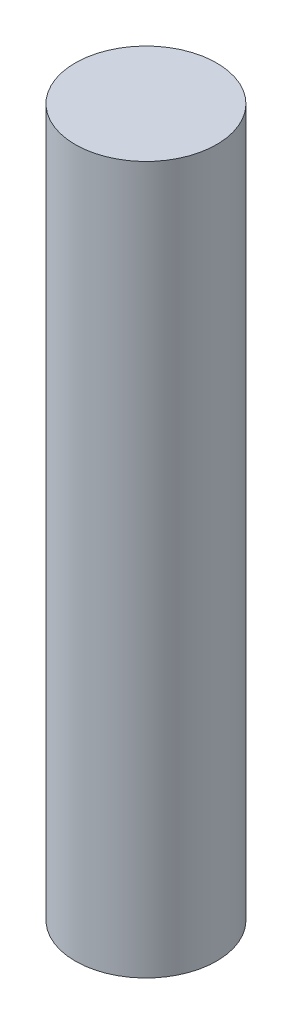
SolidWorks part; units mm, degrees
ref_plane "Front Plane" through (0, 0, 0) normal (0, 0, 1) x (1, 0, 0)
ref_plane "Top Plane" through (0, 0, 0) normal (0, 1, 0) x (1, 0, 0)
ref_plane "Right Plane" through (0, 0, 0) normal (1, 0, 0) x (0, 0, -1)
sketch "Sketch1" plane through (0, 0, 0) normal (0, 1, 0) x (1, 0, 0)
  circle A0 centre (0, 0) radius 10
extrude "Boss-Extrude1" add sketch "Sketch1" along normal blind 100 contours A0
